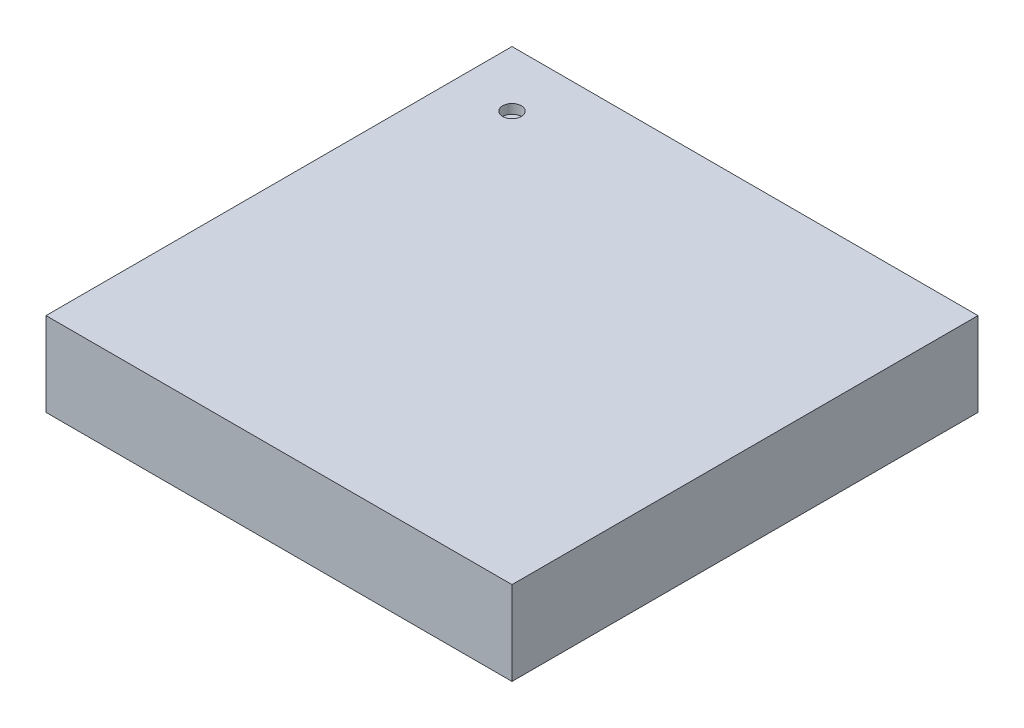
SolidWorks part; units mm, degrees
ref_plane "Plan de face" through (0, 0, 0) normal (0, 0, 1) x (1, 0, 0)
ref_plane "Plan de dessus" through (0, 0, 0) normal (0, 1, 0) x (1, 0, 0)
ref_plane "Plan de droite" through (0, 0, 0) normal (1, 0, 0) x (0, 0, -1)
sketch "Esquisse1" plane through (0, 0, 0) normal (0, 1, 0) x (1, 0, 0)
  line L1 (0, 0) -> (5, 0)
  line L2 (0, 0) -> (0, 5)
  line L3 (0, 5) -> (5, 5)
  line L4 (5, 0) -> (5, 5)
  dimension "D1" = 5
  dimension "D2" = 5
extrude "Boss.-Extru.1" add sketch "Esquisse1" along normal blind 0.9
sketch "Esquisse2" plane through (0, 0.9, 0) normal (0, 1, 0) x (1, 0, 0)
  line L0 (5, 5) -> (0, 5) construction
  line L1 (0, 5) -> (0, 0) construction
  circle A0 centre (0.6, 4.4) radius 0.1
  dimension "D1" = 0.2
  dimension "D2" = 0.6
  dimension "D3" = 0.6
extrude "Enlèv. mat.-Extru.1" cut sketch "Esquisse2" against normal blind 0.1
